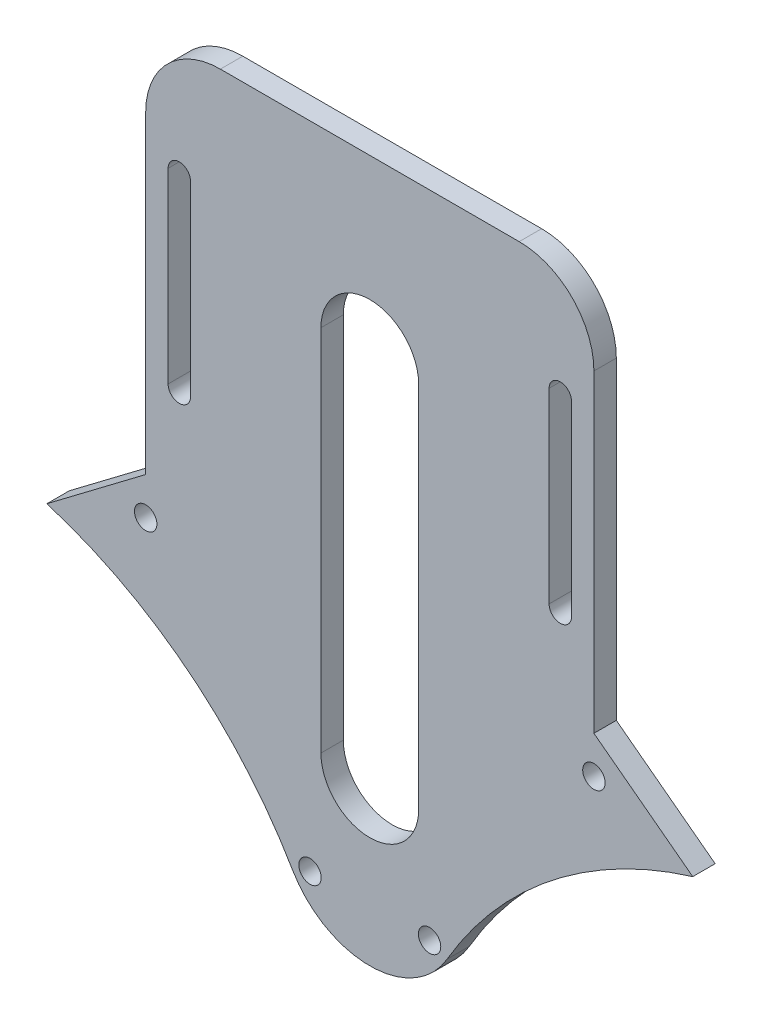
SolidWorks part; units mm, degrees
ref_plane "前视基准面" through (0, 0, 0) normal (0, 0, 1) x (1, 0, 0)
ref_plane "上视基准面" through (0, 0, 0) normal (0, 1, 0) x (1, 0, 0)
ref_plane "右视基准面" through (0, 0, 0) normal (1, 0, 0) x (0, 0, -1)
sketch "草图1" plane through (0, 0, 0) normal (0, 0, 1) x (1, 0, 0)
  line L1 (-37.42, 35) -> (37.42, 35) construction
  line L2 (30, 65) -> (43.2295, 55)
  line L3 (60, 65) -> (-60, 65) construction
  line L7 (0, 35) -> (0, 44.4384) construction
  line L8 (-30, 65) -> (-43.2295, 55)
  line L9 (30, 65) -> (30, 107)
  line L10 (20, 117) -> (-20, 117)
  line L11 (-30, 107) -> (-30, 65)
  line L12 (-60, 47) -> (60, 47) construction
  line L13 (25.5, 102) -> (25.5, 77) construction
  line L14 (27, 102) -> (27, 77)
  line L15 (24, 102) -> (24, 77)
  line L16 (-25.5, 102) -> (-25.5, 77) construction
  line L17 (-27, 102) -> (-27, 77)
  line L18 (-24, 102) -> (-24, 77)
  line L19 (0, 44.4384) -> (0, 93.7489) construction
  line L20 (-6.5418, 44.4384) -> (-6.5418, 93.7489)
  line L21 (6.5418, 44.4384) -> (6.5418, 93.7489)
  circle A0 centre (60, 0) radius 57.5 construction
  arc A1 (43.2295, 55) -> (10.3327, 28.9726) centre (60, 0) ccw
  arc A4 (-10.3327, 28.9726) -> (10.3327, 28.9726) centre (0, 35) ccw
  arc A5 (43.2295, 55) -> (59.2963, 93.7489) centre (100.7184, 53.8683) cw
  arc A6 (-43.2295, 55) -> (-10.3327, 28.9726) centre (-60, 0) cw
  arc A7 (-30, 107) -> (-20, 117) centre (-20, 107) cw
  arc A8 (20, 117) -> (30, 107) centre (20, 107) cw
  arc A9 (27, 102) -> (24, 102) centre (25.5, 102) ccw
  arc A10 (24, 77) -> (27, 77) centre (25.5, 77) ccw
  arc A11 (-27, 102) -> (-24, 102) centre (-25.5, 102) cw
  arc A12 (-24, 77) -> (-27, 77) centre (-25.5, 77) cw
  arc A13 (-6.5418, 44.4384) -> (6.5418, 44.4384) centre (0, 44.4384) ccw
  arc A14 (6.5418, 93.7489) -> (-6.5418, 93.7489) centre (0, 93.7489) ccw
  circle A15 centre (-30, 60) radius 1.5
  circle A16 centre (-8, 30) radius 1.5
  circle A17 centre (8, 30) radius 1.5
  circle A18 centre (30, 60) radius 1.5
  point P28 (25.5, 89.5)
  point P35 (-25.5, 89.5)
  point P40 (0, 69.0937)
  dimension "D1" = 60
  dimension "D4" = 10
  dimension "D2" = 10
  dimension "D3" = 70
  dimension "D5" = 3
  dimension "D6" = 25
  dimension "D7" = 9
  dimension "D8" = 5
extrude "凸台-拉伸1" add sketch "草图1" along normal blind 3 contours A8 L10 A7 L11 L8 A6 A4 A1 L2 L9 A14 L21 A13 L20 A10 L15 A9 L14 L18 A12 L17 A11
